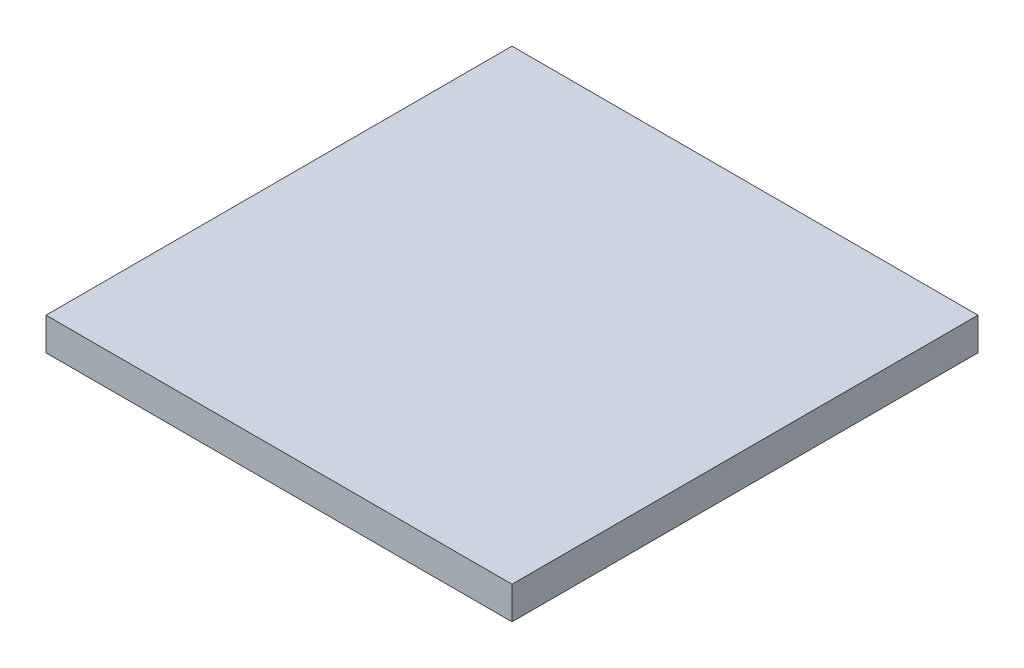
SolidWorks part; units mm, degrees
ref_plane "Plan de face" through (0, 0, 0) normal (0, 0, 1) x (1, 0, 0)
ref_plane "Plan de dessus" through (0, 0, 0) normal (0, 1, 0) x (1, 0, 0)
ref_plane "Plan de droite" through (0, 0, 0) normal (1, 0, 0) x (0, 0, -1)
sketch "Esquisse1" plane through (0, 0, 0) normal (0, 1, 0) x (1, 0, 0)
  line L1 (-250, -250) -> (250, -250)
  line L2 (-250, -250) -> (-250, 250)
  line L3 (-250, 250) -> (250, 250)
  line L4 (250, -250) -> (250, 250)
  line L5 (-250, -250) -> (250, 250) construction
  line L6 (-250, 250) -> (250, -250) construction
  point P0 (0, 0)
  dimension "D1" = 500
extrude "Boss.-Extru.1" add sketch "Esquisse1" against normal blind 35
